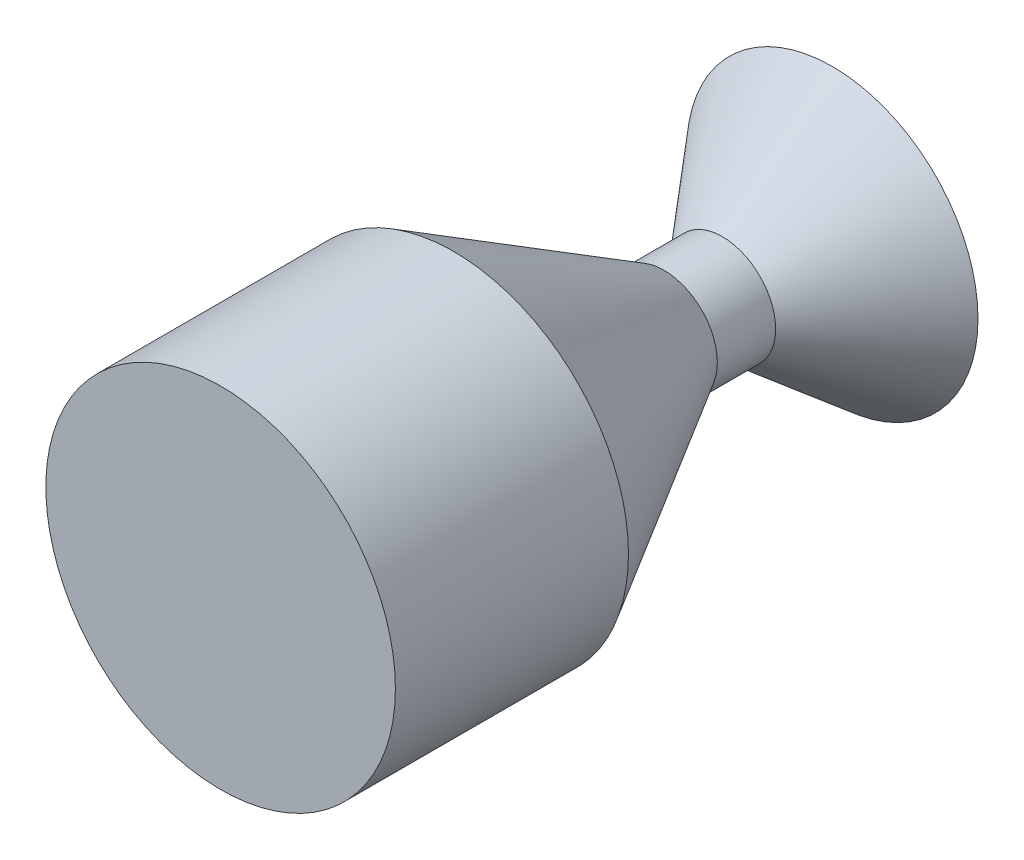
SolidWorks part; units mm, degrees
ref_plane "Front Plane" through (0, 0, 0) normal (0, 0, 1) x (1, 0, 0)
ref_plane "Top Plane" through (0, 0, 0) normal (0, 1, 0) x (1, 0, 0)
ref_plane "Right Plane" through (0, 0, 0) normal (1, 0, 0) x (0, 0, -1)
sketch "Sketch1" plane through (0, 0, 0) normal (0, 1, 0) x (1, 0, 0)
  line L0 (0, 0) -> (0, 105)
  line L1 (0, 105) -> (25, 105)
  line L2 (25, 105) -> (9.1509, 86.1117)
  line L3 (9.1509, 86.1117) -> (9.1509, 76.1117)
  line L5 (30, 0) -> (0, 0)
  line L6 (9.1509, 76.1117) -> (30, 40)
  line L7 (30, 40) -> (30, 0)
  dimension "D1" = 105
  dimension "D2" = 50
  dimension "D3" = 60
  dimension "D4" = 10
  dimension "D5" = 25
  dimension "D6" = 30
  dimension "D7" = 40
revolve "Revolve1" add sketch "Sketch1" angle 360 about L0
